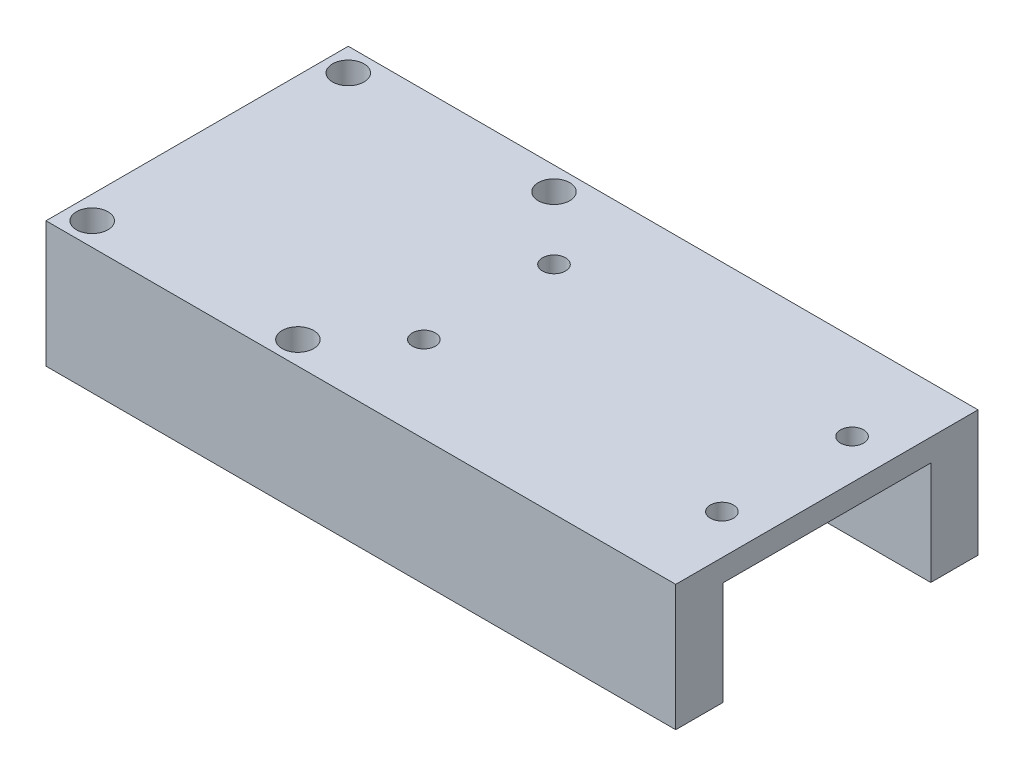
SolidWorks part; units mm, degrees
ref_plane "Front Plane" through (0, 0, 0) normal (0, 0, 1) x (1, 0, 0)
ref_plane "Top Plane" through (0, 0, 0) normal (0, 1, 0) x (1, 0, 0)
ref_plane "Right Plane" through (0, 0, 0) normal (1, 0, 0) x (0, 0, -1)
sketch "Sketch1" plane through (0, 0, 0) normal (0, 1, 0) x (1, 0, 0)
  line L1 (-15, -18) -> (15, -18)
  line L2 (-15, -18) -> (-15, 18)
  line L3 (-15, 18) -> (15, 18)
  line L4 (15, -18) -> (15, 18)
  line L5 (-15, -18) -> (15, 18) construction
  line L6 (-15, 18) -> (15, -18) construction
  point P0 (0, 0)
  dimension "D1" = 30
  dimension "D2" = 36
extrude "Boss-Extrude1" add sketch "Sketch1" along normal blind 30
sketch "Sketch3" plane through (15, 0, 0) normal (1, 0, 0) x (0, 0, -1)
  line L0 (0, 0) -> (0, 30) construction
  line L1 (-18, 0) -> (18, 0) construction
  line L2 (-18, 30) -> (18, 30) construction
  circle A0 centre (0, 15) radius 12.375
  dimension "D1" = 24.75
extrude "Cut-Extrude1" cut sketch "Sketch3" against normal blind 40
sketch "Sketch5" plane through (0, 30, 0) normal (0, 1, 0) x (1, 0, 0)
  line L7 (15, 18) -> (-15, 18) construction
  line L9 (-15, 18) -> (-15, -18) construction
  line L10 (0, 0) -> (0, 2.7791) construction
  line L11 (0, 2.7791) -> (0, 0) construction
  line L12 (0, 0) -> (-2.7536, 0) construction
  circle A1 centre (-12.25, 15.25) radius 1.875
  circle A2 centre (-12.25, -15.25) radius 1.875
  circle A3 centre (12.25, -15.25) radius 1.875
  circle A4 centre (12.25, 15.25) radius 1.875
  point P0 (0, 0)
  dimension "D2" = 3.75
  dimension "D3" = 2.75
  dimension "D4" = 2.75
extrude "Cut-Extrude2" cut sketch "Sketch5" against normal blind 40
sketch "Sketch7" plane through (0, 0, 0) normal (1, 0, 0) x (0, 0, -1)
  line L0 (-18, 30) -> (-18, 0) construction
  line L1 (-18, 15) -> (18, 15)
  line L2 (-18, 15) -> (-18, 0)
  line L3 (-18, 0) -> (18, 0)
  line L4 (18, 15) -> (18, 0)
extrude "Cut-Extrude3" cut sketch "Sketch7" against normal through all from surface at 15 starting at face at (15, 15, -12.375)
sketch "Sketch8" plane through (15, 0, 0) normal (1, 0, 0) x (0, 0, -1)
  line L0 (18, 30) -> (18, 15) construction
  line L1 (-18, 30) -> (18, 30)
  line L2 (-18, 30) -> (-18, 27.3314)
  line L3 (-12.375, 27.3314) -> (12.375, 27.3314)
  line L4 (18, 30) -> (18, 27.3314)
  line L5 (-12.375, 15) -> (-18, 15) construction
  line L6 (-18, 15) -> (-12.375, 15)
  line L7 (-18, 15) -> (-18, 27.3314)
  line L9 (-12.375, 15) -> (-12.375, 27.3314)
  line L12 (18, 27.3314) -> (18, 15)
  line L13 (18, 15) -> (12.375, 15)
  line L14 (12.375, 27.3314) -> (12.375, 15)
  arc A0 (12.375, 15) -> (-12.375, 15) centre (0, 15) ccw construction
extrude "Boss-Extrude2" add sketch "Sketch8" along normal blind 45
sketch "Sketch9" plane through (0, 30, 0) normal (0, 1, 0) x (1, 0, 0)
  line L0 (15, 0) -> (60, 0) construction
  line L1 (60, 18) -> (60, -18) construction
  line L2 (15, 18) -> (15, -18) construction
  line L3 (60, 18) -> (-15, 18) construction
  line L4 (-15, -18) -> (60, -18) construction
  line L5 (-15, 18) -> (-15, -18) construction
  line L6 (17.5, 0) -> (17.5, 10) construction
  line L7 (17.5, -10) -> (57.5, -10) construction
  line L8 (17.5, -10) -> (17.5, 0) construction
  line L9 (17.5, 10) -> (57.5, 10) construction
  line L10 (57.5, -10) -> (57.5, 0) construction
  line L11 (57.5, 0) -> (57.5, 10) construction
  line L12 (37.5, 0) -> (37.5, 1.845) construction
  line L13 (19.75, 7.75) -> (17.5, 7.75) construction
  circle A7 centre (19.75, 7.75) radius 1.375
  circle A8 centre (19.75, -7.75) radius 1.375
  circle A9 centre (55.25, -7.75) radius 1.375
  circle A10 centre (55.25, 7.75) radius 1.375
  point P0 (37.5, 0)
  point P24 (37.5, 0)
  dimension "D4" = 2.75
  dimension "D1" = 30
extrude "Cut-Extrude4" cut sketch "Sketch9" against normal blind 10
